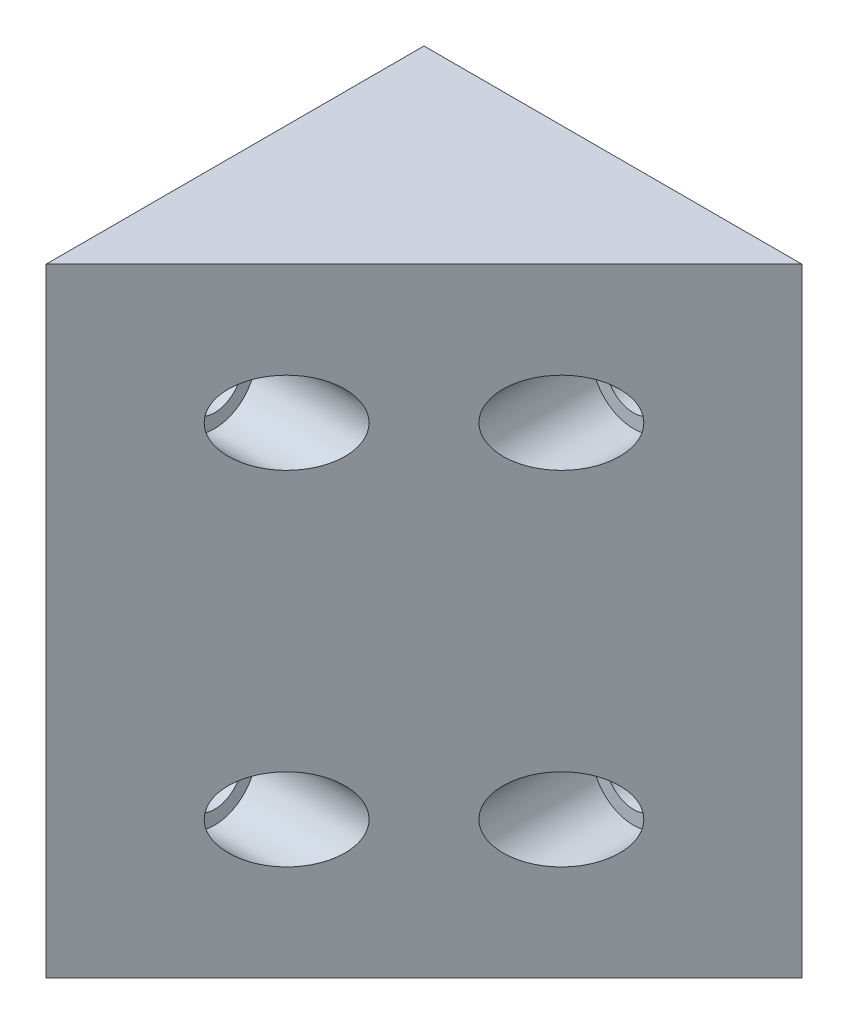
SolidWorks part; units mm, degrees
ref_plane "Front Plane" through (0, 0, 0) normal (0, 0, 1) x (1, 0, 0)
ref_plane "Top Plane" through (0, 0, 0) normal (0, 1, 0) x (1, 0, 0)
ref_plane "Right Plane" through (0, 0, 0) normal (1, 0, 0) x (0, 0, -1)
sketch "Sketch1" plane through (0, 0, 0) normal (0, 1, 0) x (1, 0, 0)
  line L0 (0, 0) -> (55, 55)
  line L2 (0, 0) -> (0, 55)
  line L3 (0, 55) -> (55, 55)
  dimension "D1" = 55
  dimension "D2" = 55
extrude "Boss-Extrude1" add sketch "Sketch1" along normal blind 100
ref_plane "Plane1" through (50, 0, 0) normal (1, 0, 0) x (0, 0, -1)
ref_plane "Plane2" through (27.5, 0, -27.5) normal (-0.7071, 0, 0.7071) x (0, -1, 0)
sketch "Sketch2" plane through (50, 0, 0) normal (1, 0, 0) x (0, 0, -1)
  circle A0 centre (17.5, 25) radius 6
  circle A1 centre (17.5, 75) radius 6
extrude "Cut-Extrude1" cut sketch "Sketch2" against normal blind 43
sketch "Sketch4" plane through (7, 0, 0) normal (1, 0, 0) x (0, 0, -1)
  circle A0 centre (17.5, 75) radius 4
  circle A1 centre (17.5, 25) radius 4
extrude "Cut-Extrude2" cut sketch "Sketch4" against normal up to surface (7 mm away) up to face at (0, 50, -27.5)
mirror "Mirror6" about plane through (27.5, 0, -27.5) normal (-0.7071, 0, 0.7071) of "Cut-Extrude1"
sketch "Sketch6" plane through (0, 0, -48) normal (0, 0, 1) x (1, 0, 0)
  circle A0 centre (37.5, 75) radius 4
  circle A1 centre (37.5, 25) radius 4
extrude "Cut-Extrude3" cut sketch "Sketch6" against normal up to surface (7 mm away) up to face at (27.5, 50, -55)
sketch "Sketch7" plane through (0, 0, 0) normal (0, 0, 1) x (1, 0, 0)
  line L0 (55, 100) -> (55, 0) construction
  line L1 (0, 100) -> (55, 100)
  line L2 (0, 100) -> (0, 95)
  line L3 (0, 95) -> (55, 95)
  line L4 (55, 100) -> (55, 95)
  line L6 (0, 0) -> (55, 0)
  line L7 (0, 0) -> (0, 5)
  line L8 (0, 5) -> (55, 5)
  line L9 (55, 0) -> (55, 5)
extrude "Cut-Extrude4" cut sketch "Sketch7" against normal up to surface (55 mm away) up to face at (41.5, 75, -55)
